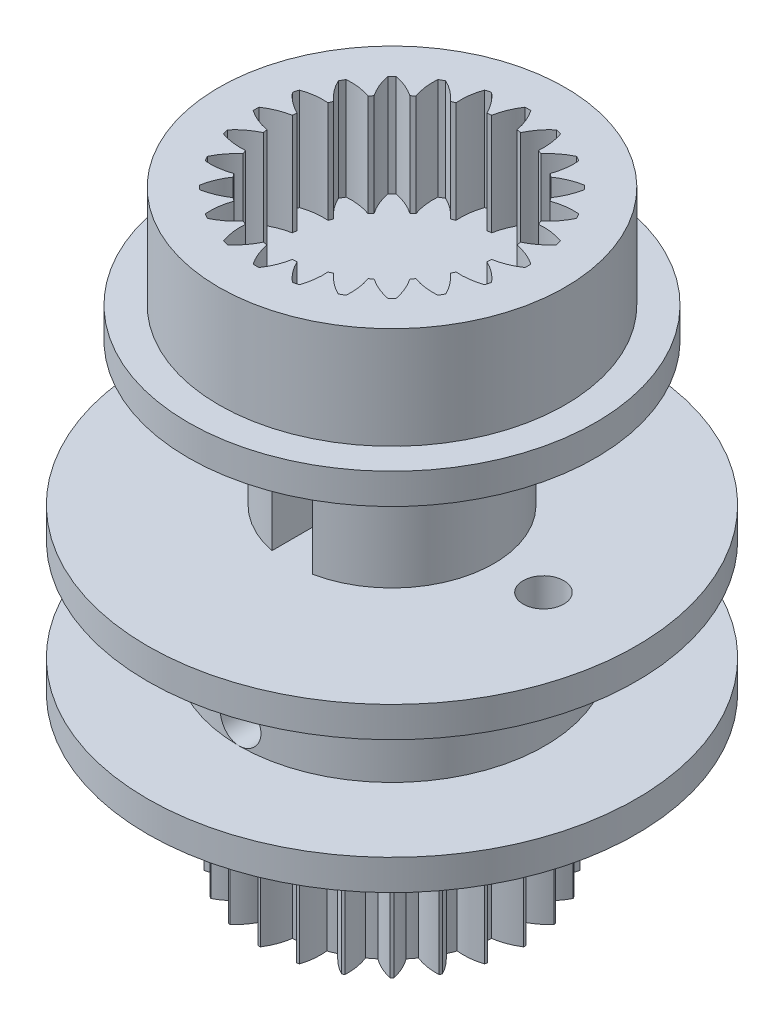
SolidWorks part; units mm, degrees
ref_plane "Front Plane" through (0, 0, 0) normal (0, 0, 1) x (1, 0, 0)
ref_plane "Top Plane" through (0, 0, 0) normal (0, 1, 0) x (1, 0, 0)
ref_plane "Right Plane" through (0, 0, 0) normal (1, 0, 0) x (0, 0, -1)
sketch "Sketch1" plane through (0, 0, 0) normal (0, 1, 0) x (1, 0, 0)
  arc A1 (17.6435, -5.4958) -> (17.2147, -6.6437) centre (20.0844, -7.0617) ccw
  arc A2 (17.2147, -6.6437) -> (16.7858, -6.7002) centre (17.7045, -12.0215) ccw
  arc A3 (16.7858, -6.7002) -> (16.0745, -5.7023) centre (14.122, -7.8467) ccw
  arc A4 (16.0745, -5.7023) -> (15.9566, -5.7339) centre (17.7045, -12.0215) ccw
  arc A5 (15.9566, -5.7339) -> (15.8395, -6.9538) centre (18.7196, -6.6147) ccw
  arc A6 (15.8395, -6.9538) -> (15.4399, -7.1193) centre (17.7045, -12.0215) ccw
  arc A7 (15.4399, -7.1193) -> (14.4945, -6.3396) centre (13.1636, -8.9161) ccw
  arc A8 (14.4945, -6.3396) -> (14.3888, -6.4005) centre (17.7045, -12.0215) ccw
  arc A9 (14.3888, -6.4005) -> (14.5914, -7.6091) centre (17.2857, -6.5362) ccw
  arc A10 (14.5914, -7.6091) -> (14.2483, -7.8725) centre (17.7045, -12.0215) ccw
  arc A11 (14.2483, -7.8725) -> (13.1333, -7.364) centre (12.5146, -10.1972) ccw
  arc A12 (13.1333, -7.364) -> (13.047, -7.4502) centre (17.7045, -12.0215) ccw
  arc A13 (13.047, -7.4502) -> (13.5555, -8.5652) centre (15.8802, -6.8315) ccw
  arc A14 (13.5555, -8.5652) -> (13.2922, -8.9084) centre (17.7045, -12.0215) ccw
  arc A15 (13.2922, -8.9084) -> (12.0836, -8.7058) centre (12.2193, -11.6026) ccw
  arc A16 (12.0836, -8.7058) -> (12.0226, -8.8114) centre (17.7045, -12.0215) ccw
  arc A17 (12.0226, -8.8114) -> (12.8023, -9.7568) centre (14.5992, -7.4805) ccw
  arc A18 (12.8023, -9.7568) -> (12.6368, -10.1565) centre (17.7045, -12.0215) ccw
  arc A19 (12.6368, -10.1565) -> (11.4169, -10.2736) centre (12.2978, -13.0366) ccw
  arc A20 (11.4169, -10.2736) -> (11.3854, -10.3914) centre (17.7045, -12.0215) ccw
  arc A21 (11.3854, -10.3914) -> (12.3832, -11.1028) centre (13.5297, -8.439) ccw
  arc A22 (12.3832, -11.1028) -> (12.3268, -11.5316) centre (17.7045, -12.0215) ccw
  arc A23 (12.3268, -11.5316) -> (11.1788, -11.9605) centre (12.7447, -14.4014) ccw
  arc A24 (11.1788, -11.9605) -> (11.1788, -12.0825) centre (17.7045, -12.0215) ccw
  arc A25 (11.1788, -12.0825) -> (12.3268, -12.5113) centre (12.7447, -9.6416) ccw
  arc A26 (12.3268, -12.5113) -> (12.3832, -12.9402) centre (17.7045, -12.0215) ccw
  arc A27 (12.3832, -12.9402) -> (11.3854, -13.6515) centre (13.5297, -15.604) ccw
  arc A28 (11.3854, -13.6515) -> (11.4169, -13.7694) centre (17.7045, -12.0215) ccw
  arc A29 (11.4169, -13.7694) -> (12.6368, -13.8865) centre (12.2978, -11.0064) ccw
  arc A30 (12.6368, -13.8865) -> (12.8023, -14.2861) centre (17.7045, -12.0215) ccw
  arc A31 (12.8023, -14.2861) -> (12.0226, -15.2315) centre (14.5992, -16.5624) ccw
  arc A32 (12.0226, -15.2315) -> (12.0836, -15.3372) centre (17.7045, -12.0215) ccw
  arc A33 (12.0836, -15.3372) -> (13.2922, -15.1346) centre (12.2193, -12.4403) ccw
  arc A34 (13.2922, -15.1346) -> (13.5555, -15.4777) centre (17.7045, -12.0215) ccw
  arc A35 (13.5555, -15.4777) -> (13.047, -16.5927) centre (15.8802, -17.2114) ccw
  arc A36 (13.047, -16.5927) -> (13.1333, -16.679) centre (17.7045, -12.0215) ccw
  arc A37 (13.1333, -16.679) -> (14.2483, -16.1705) centre (12.5146, -13.8458) ccw
  arc A38 (14.2483, -16.1705) -> (14.5914, -16.4338) centre (17.7045, -12.0215) ccw
  arc A39 (14.5914, -16.4338) -> (14.3888, -17.6424) centre (17.2857, -17.5067) ccw
  arc A40 (14.3888, -17.6424) -> (14.4945, -17.7034) centre (17.7045, -12.0215) ccw
  arc A41 (14.4945, -17.7034) -> (15.4399, -16.9237) centre (13.1636, -15.1268) ccw
  arc A42 (15.4399, -16.9237) -> (15.8395, -17.0892) centre (17.7045, -12.0215) ccw
  arc A43 (15.8395, -17.0892) -> (15.9566, -18.3091) centre (18.7196, -17.4282) ccw
  arc A44 (15.9566, -18.3091) -> (16.0745, -18.3406) centre (17.7045, -12.0215) ccw
  arc A45 (16.0745, -18.3406) -> (16.7858, -17.3428) centre (14.122, -16.1963) ccw
  arc A46 (16.7858, -17.3428) -> (17.2147, -17.3992) centre (17.7045, -12.0215) ccw
  arc A47 (17.2147, -17.3992) -> (17.6435, -18.5472) centre (20.0844, -16.9813) ccw
  arc A48 (17.6435, -18.5472) -> (17.7655, -18.5472) centre (17.7045, -12.0215) ccw
  arc A49 (17.7655, -18.5472) -> (18.1944, -17.3992) centre (15.3246, -16.9813) ccw
  arc A50 (18.1944, -17.3992) -> (18.6232, -17.3428) centre (17.7045, -12.0215) ccw
  arc A51 (18.6232, -17.3428) -> (19.3346, -18.3406) centre (21.287, -16.1963) ccw
  arc A52 (19.3346, -18.3406) -> (19.4524, -18.3091) centre (17.7045, -12.0215) ccw
  arc A53 (19.4524, -18.3091) -> (19.5695, -17.0892) centre (16.6894, -17.4282) ccw
  arc A54 (19.5695, -17.0892) -> (19.9692, -16.9237) centre (17.7045, -12.0215) ccw
  arc A55 (19.9692, -16.9237) -> (20.9146, -17.7034) centre (22.2455, -15.1268) ccw
  arc A56 (20.9146, -17.7034) -> (21.0202, -17.6424) centre (17.7045, -12.0215) ccw
  arc A57 (21.0202, -17.6424) -> (20.8176, -16.4338) centre (18.1234, -17.5067) ccw
  arc A58 (20.8176, -16.4338) -> (21.1608, -16.1705) centre (17.7045, -12.0215) ccw
  arc A59 (21.1608, -16.1705) -> (22.2758, -16.679) centre (22.8945, -13.8458) ccw
  arc A60 (22.2758, -16.679) -> (22.362, -16.5927) centre (17.7045, -12.0215) ccw
  arc A61 (22.362, -16.5927) -> (21.8535, -15.4777) centre (19.5288, -17.2114) ccw
  arc A62 (21.8535, -15.4777) -> (22.1169, -15.1346) centre (17.7045, -12.0215) ccw
  arc A63 (22.1169, -15.1346) -> (23.3255, -15.3372) centre (23.1898, -12.4403) ccw
  arc A64 (23.3255, -15.3372) -> (23.3864, -15.2315) centre (17.7045, -12.0215) ccw
  arc A65 (23.3864, -15.2315) -> (22.6067, -14.2861) centre (20.8099, -16.5624) ccw
  arc A66 (22.6067, -14.2861) -> (22.7722, -13.8865) centre (17.7045, -12.0215) ccw
  arc A67 (22.7722, -13.8865) -> (23.9921, -13.7694) centre (23.1113, -11.0064) ccw
  arc A68 (23.9921, -13.7694) -> (24.0237, -13.6515) centre (17.7045, -12.0215) ccw
  arc A69 (24.0237, -13.6515) -> (23.0258, -12.9402) centre (21.8793, -15.604) ccw
  arc A70 (23.0258, -12.9402) -> (23.0823, -12.5113) centre (17.7045, -12.0215) ccw
  arc A71 (23.0823, -12.5113) -> (24.2302, -12.0825) centre (22.6643, -9.6416) ccw
  arc A72 (24.2302, -12.0825) -> (24.2302, -11.9605) centre (17.7045, -12.0215) ccw
  arc A73 (24.2302, -11.9605) -> (23.0823, -11.5316) centre (22.6643, -14.4014) ccw
  arc A74 (23.0823, -11.5316) -> (23.0258, -11.1028) centre (17.7045, -12.0215) ccw
  arc A75 (23.0258, -11.1028) -> (24.0237, -10.3914) centre (21.8793, -8.439) ccw
  arc A76 (24.0237, -10.3914) -> (23.9921, -10.2736) centre (17.7045, -12.0215) ccw
  arc A77 (23.9921, -10.2736) -> (22.7722, -10.1565) centre (23.1113, -13.0366) ccw
  arc A78 (22.7722, -10.1565) -> (22.6067, -9.7568) centre (17.7045, -12.0215) ccw
  arc A79 (22.6067, -9.7568) -> (23.3864, -8.8114) centre (20.8099, -7.4805) ccw
  arc A80 (23.3864, -8.8114) -> (23.3255, -8.7058) centre (17.7045, -12.0215) ccw
  arc A81 (23.3255, -8.7058) -> (22.1169, -8.9084) centre (23.1898, -11.6026) ccw
  arc A82 (22.1169, -8.9084) -> (21.8535, -8.5652) centre (17.7045, -12.0215) ccw
  arc A83 (21.8535, -8.5652) -> (22.362, -7.4502) centre (19.5288, -6.8315) ccw
  arc A84 (22.362, -7.4502) -> (22.2758, -7.364) centre (17.7045, -12.0215) ccw
  arc A85 (22.2758, -7.364) -> (21.1608, -7.8725) centre (22.8945, -10.1972) ccw
  arc A86 (21.1608, -7.8725) -> (20.8176, -7.6091) centre (17.7045, -12.0215) ccw
  arc A87 (20.8176, -7.6091) -> (21.0202, -6.4005) centre (18.1234, -6.5362) ccw
  arc A88 (21.0202, -6.4005) -> (20.9146, -6.3396) centre (17.7045, -12.0215) ccw
  arc A89 (20.9146, -6.3396) -> (19.9692, -7.1193) centre (22.2455, -8.9161) ccw
  arc A90 (19.9692, -7.1193) -> (19.5695, -6.9538) centre (17.7045, -12.0215) ccw
  arc A91 (19.5695, -6.9538) -> (19.4524, -5.7339) centre (16.6894, -6.6147) ccw
  arc A92 (19.4524, -5.7339) -> (19.3346, -5.7023) centre (17.7045, -12.0215) ccw
  arc A93 (19.3346, -5.7023) -> (18.6232, -6.7002) centre (21.287, -7.8467) ccw
  arc A94 (18.6232, -6.7002) -> (18.1944, -6.6437) centre (17.7045, -12.0215) ccw
  arc A95 (18.1944, -6.6437) -> (17.7655, -5.4958) centre (15.3246, -7.0617) ccw
  arc A96 (17.7655, -5.4958) -> (17.6435, -5.4958) centre (17.7045, -12.0215) ccw
extrude "Boss-Extrude1" add sketch "Sketch1" along normal blind 7.5
sketch "Sketch2" plane through (0, 7.5, 0) normal (0, 1, 0) x (1, 0, 0)
  circle A0 centre (17.7045, -12.0215) radius 12
  dimension "D1" = 24
extrude "Boss-Extrude2" add sketch "Sketch2" along normal blind 1.5
sketch "Sketch3" plane through (0, 9, 0) normal (0, 1, 0) x (1, 0, 0)
  circle A0 centre (17.7045, -12.0215) radius 7.5
  dimension "D1" = 15
extrude "Boss-Extrude3" add sketch "Sketch3" along normal blind 5
sketch "Sketch4" plane through (0, 14, 0) normal (0, 1, 0) x (1, 0, 0)
  circle A0 centre (17.7045, -12.0215) radius 12
  dimension "D1" = 24
extrude "Boss-Extrude4" add sketch "Sketch4" along normal blind 1.5
sketch "Sketch6" plane through (0, 15.5, 0) normal (0, 1, 0) x (1, 0, 0)
  circle A1 centre (17.7045, -12.0215) radius 5
  dimension "D1" = 10
extrude "Boss-Extrude5" add sketch "Sketch6" along normal blind 7
sketch "Sketch9" plane through (0, 22.5, 0) normal (0, 1, 0) x (1, 0, 0)
  circle A0 centre (17.7045, -12.0215) radius 10
extrude "Boss-Extrude6" add sketch "Sketch9" along normal blind 1.5 contours A0
sketch "Sketch11" plane through (0, 24, 0) normal (0, 1, 0) x (1, 0, 0)
  arc A0 (17.847, -5.347) -> (17.562, -5.347) centre (17.7045, -12.0215) ccw
  arc A1 (17.562, -5.347) -> (17.0854, -6.5061) centre (20.0844, -7.0617) ccw
  arc A2 (17.0854, -6.5061) -> (16.875, -6.5338) centre (17.7045, -12.0215) ccw
  arc A3 (16.875, -6.5338) -> (16.1147, -5.5376) centre (14.122, -7.8467) ccw
  arc A4 (16.1147, -5.5376) -> (15.8394, -5.6113) centre (17.7045, -12.0215) ccw
  arc A5 (15.8394, -5.6113) -> (15.679, -6.8543) centre (18.7196, -6.6147) ccw
  arc A6 (15.679, -6.8543) -> (15.483, -6.9355) centre (17.7045, -12.0215) ccw
  arc A7 (15.483, -6.9355) -> (14.4907, -6.17) centre (13.1636, -8.9161) ccw
  arc A8 (14.4907, -6.17) -> (14.2439, -6.3125) centre (17.7045, -12.0215) ccw
  arc A9 (14.2439, -6.3125) -> (14.4107, -7.5546) centre (17.2857, -6.5362) ccw
  arc A10 (14.4107, -7.5546) -> (14.2423, -7.6838) centre (17.7045, -12.0215) ccw
  arc A11 (14.2423, -7.6838) -> (13.0857, -7.2012) centre (12.5146, -10.1972) ccw
  arc A12 (13.0857, -7.2012) -> (12.8842, -7.4027) centre (17.7045, -12.0215) ccw
  arc A13 (12.8842, -7.4027) -> (13.3668, -8.5593) centre (15.8802, -6.8315) ccw
  arc A14 (13.3668, -8.5593) -> (13.2376, -8.7277) centre (17.7045, -12.0215) ccw
  arc A15 (13.2376, -8.7277) -> (11.9955, -8.5608) centre (12.2193, -11.6026) ccw
  arc A16 (11.9955, -8.5608) -> (11.853, -8.8076) centre (17.7045, -12.0215) ccw
  arc A17 (11.853, -8.8076) -> (12.6185, -9.7999) centre (14.5992, -7.4805) ccw
  arc A18 (12.6185, -9.7999) -> (12.5373, -9.996) centre (17.7045, -12.0215) ccw
  arc A19 (12.5373, -9.996) -> (11.2943, -10.1564) centre (12.2978, -13.0366) ccw
  arc A20 (11.2943, -10.1564) -> (11.2206, -10.4316) centre (17.7045, -12.0215) ccw
  arc A21 (11.2206, -10.4316) -> (12.2169, -11.192) centre (13.5297, -8.439) ccw
  arc A22 (12.2169, -11.192) -> (12.1892, -11.4024) centre (17.7045, -12.0215) ccw
  arc A23 (12.1892, -11.4024) -> (11.03, -11.879) centre (12.7447, -14.4014) ccw
  arc A24 (11.03, -11.879) -> (11.03, -12.164) centre (17.7045, -12.0215) ccw
  arc A25 (11.03, -12.164) -> (12.1892, -12.6406) centre (12.7447, -9.6416) ccw
  arc A26 (12.1892, -12.6406) -> (12.2169, -12.851) centre (17.7045, -12.0215) ccw
  arc A27 (12.2169, -12.851) -> (11.2206, -13.6113) centre (13.5297, -15.604) ccw
  arc A28 (11.2206, -13.6113) -> (11.2943, -13.8866) centre (17.7045, -12.0215) ccw
  arc A29 (11.2943, -13.8866) -> (12.5373, -14.047) centre (12.2978, -11.0064) ccw
  arc A30 (12.5373, -14.047) -> (12.6185, -14.243) centre (17.7045, -12.0215) ccw
  arc A31 (12.6185, -14.243) -> (11.853, -15.2353) centre (14.5992, -16.5624) ccw
  arc A32 (11.853, -15.2353) -> (11.9955, -15.4821) centre (17.7045, -12.0215) ccw
  arc A33 (11.9955, -15.4821) -> (13.2376, -15.3153) centre (12.2193, -12.4403) ccw
  arc A34 (13.2376, -15.3153) -> (13.3668, -15.4837) centre (17.7045, -12.0215) ccw
  arc A35 (13.3668, -15.4837) -> (12.8842, -16.6403) centre (15.8802, -17.2114) ccw
  arc A36 (12.8842, -16.6403) -> (13.0857, -16.8418) centre (17.7045, -12.0215) ccw
  arc A37 (13.0857, -16.8418) -> (14.2423, -16.3592) centre (12.5146, -13.8458) ccw
  arc A38 (14.2423, -16.3592) -> (14.4107, -16.4884) centre (17.7045, -12.0215) ccw
  arc A39 (14.4107, -16.4884) -> (14.2439, -17.7305) centre (17.2857, -17.5067) ccw
  arc A40 (14.2439, -17.7305) -> (14.4907, -17.873) centre (17.7045, -12.0215) ccw
  arc A41 (14.4907, -17.873) -> (15.483, -17.1075) centre (13.1636, -15.1268) ccw
  arc A42 (15.483, -17.1075) -> (15.679, -17.1887) centre (17.7045, -12.0215) ccw
  arc A43 (15.679, -17.1887) -> (15.8394, -18.4317) centre (18.7196, -17.4282) ccw
  arc A44 (15.8394, -18.4317) -> (16.1147, -18.5054) centre (17.7045, -12.0215) ccw
  arc A45 (16.1147, -18.5054) -> (16.875, -17.5091) centre (14.122, -16.1963) ccw
  arc A46 (16.875, -17.5091) -> (17.0854, -17.5368) centre (17.7045, -12.0215) ccw
  arc A47 (17.0854, -17.5368) -> (17.562, -18.696) centre (20.0844, -16.9813) ccw
  arc A48 (17.562, -18.696) -> (17.847, -18.696) centre (17.7045, -12.0215) ccw
  arc A49 (17.847, -18.696) -> (18.3236, -17.5368) centre (15.3246, -16.9813) ccw
  arc A50 (18.3236, -17.5368) -> (18.534, -17.5091) centre (17.7045, -12.0215) ccw
  arc A51 (18.534, -17.5091) -> (19.2944, -18.5054) centre (21.287, -16.1963) ccw
  arc A52 (19.2944, -18.5054) -> (19.5696, -18.4317) centre (17.7045, -12.0215) ccw
  arc A53 (19.5696, -18.4317) -> (19.73, -17.1887) centre (16.6894, -17.4282) ccw
  arc A54 (19.73, -17.1887) -> (19.9261, -17.1075) centre (17.7045, -12.0215) ccw
  arc A55 (19.9261, -17.1075) -> (20.9184, -17.873) centre (22.2455, -15.1268) ccw
  arc A56 (20.9184, -17.873) -> (21.1652, -17.7305) centre (17.7045, -12.0215) ccw
  arc A57 (21.1652, -17.7305) -> (20.9983, -16.4884) centre (18.1234, -17.5067) ccw
  arc A58 (20.9983, -16.4884) -> (21.1667, -16.3592) centre (17.7045, -12.0215) ccw
  arc A59 (21.1667, -16.3592) -> (22.3233, -16.8418) centre (22.8945, -13.8458) ccw
  arc A60 (22.3233, -16.8418) -> (22.5248, -16.6403) centre (17.7045, -12.0215) ccw
  arc A61 (22.5248, -16.6403) -> (22.0422, -15.4837) centre (19.5288, -17.2114) ccw
  arc A62 (22.0422, -15.4837) -> (22.1714, -15.3153) centre (17.7045, -12.0215) ccw
  arc A63 (22.1714, -15.3153) -> (23.4135, -15.4821) centre (23.1898, -12.4403) ccw
  arc A64 (23.4135, -15.4821) -> (23.556, -15.2353) centre (17.7045, -12.0215) ccw
  arc A65 (23.556, -15.2353) -> (22.7905, -14.243) centre (20.8099, -16.5624) ccw
  arc A66 (22.7905, -14.243) -> (22.8717, -14.047) centre (17.7045, -12.0215) ccw
  arc A67 (22.8717, -14.047) -> (24.1147, -13.8866) centre (23.1113, -11.0064) ccw
  arc A68 (24.1147, -13.8866) -> (24.1884, -13.6113) centre (17.7045, -12.0215) ccw
  arc A69 (24.1884, -13.6113) -> (23.1922, -12.851) centre (21.8793, -15.604) ccw
  arc A70 (23.1922, -12.851) -> (23.2199, -12.6406) centre (17.7045, -12.0215) ccw
  arc A71 (23.2199, -12.6406) -> (24.379, -12.164) centre (22.6643, -9.6416) ccw
  arc A72 (24.379, -12.164) -> (24.379, -11.879) centre (17.7045, -12.0215) ccw
  arc A73 (24.379, -11.879) -> (23.2199, -11.4024) centre (22.6643, -14.4014) ccw
  arc A74 (23.2199, -11.4024) -> (23.1922, -11.192) centre (17.7045, -12.0215) ccw
  arc A75 (23.1922, -11.192) -> (24.1884, -10.4316) centre (21.8793, -8.439) ccw
  arc A76 (24.1884, -10.4316) -> (24.1147, -10.1564) centre (17.7045, -12.0215) ccw
  arc A77 (24.1147, -10.1564) -> (22.8717, -9.996) centre (23.1113, -13.0366) ccw
  arc A78 (22.8717, -9.996) -> (22.7905, -9.7999) centre (17.7045, -12.0215) ccw
  arc A79 (22.7905, -9.7999) -> (23.556, -8.8076) centre (20.8099, -7.4805) ccw
  arc A80 (23.556, -8.8076) -> (23.4135, -8.5608) centre (17.7045, -12.0215) ccw
  arc A81 (23.4135, -8.5608) -> (22.1714, -8.7277) centre (23.1898, -11.6026) ccw
  arc A82 (22.1714, -8.7277) -> (22.0422, -8.5593) centre (17.7045, -12.0215) ccw
  arc A83 (22.0422, -8.5593) -> (22.5248, -7.4027) centre (19.5288, -6.8315) ccw
  arc A84 (22.5248, -7.4027) -> (22.3233, -7.2012) centre (17.7045, -12.0215) ccw
  arc A85 (22.3233, -7.2012) -> (21.1667, -7.6838) centre (22.8945, -10.1972) ccw
  arc A86 (21.1667, -7.6838) -> (20.9983, -7.5546) centre (17.7045, -12.0215) ccw
  arc A87 (20.9983, -7.5546) -> (21.1652, -6.3125) centre (18.1234, -6.5362) ccw
  arc A88 (21.1652, -6.3125) -> (20.9184, -6.17) centre (17.7045, -12.0215) ccw
  arc A89 (20.9184, -6.17) -> (19.9261, -6.9355) centre (22.2455, -8.9161) ccw
  arc A90 (19.9261, -6.9355) -> (19.73, -6.8543) centre (17.7045, -12.0215) ccw
  arc A91 (19.73, -6.8543) -> (19.5696, -5.6113) centre (16.6894, -6.6147) ccw
  arc A92 (19.5696, -5.6113) -> (19.2944, -5.5376) centre (17.7045, -12.0215) ccw
  arc A93 (19.2944, -5.5376) -> (18.534, -6.5338) centre (21.287, -7.8467) ccw
  arc A94 (18.534, -6.5338) -> (18.3236, -6.5061) centre (17.7045, -12.0215) ccw
  arc A95 (18.3236, -6.5061) -> (17.847, -5.347) centre (15.3246, -7.0617) ccw
  arc A96 (17.7655, -5.4958) -> (17.6435, -5.4958) centre (17.7045, -12.0215) ccw
  arc A97 (18.1944, -6.6437) -> (17.7655, -5.4958) centre (15.3246, -7.0617) ccw
  arc A98 (18.6232, -6.7002) -> (18.1944, -6.6437) centre (17.7045, -12.0215) ccw
  arc A99 (19.3346, -5.7023) -> (18.6232, -6.7002) centre (21.287, -7.8467) ccw
  arc A100 (19.4524, -5.7339) -> (19.3346, -5.7023) centre (17.7045, -12.0215) ccw
  arc A101 (19.5695, -6.9538) -> (19.4524, -5.7339) centre (16.6894, -6.6147) ccw
  arc A102 (19.9692, -7.1193) -> (19.5695, -6.9538) centre (17.7045, -12.0215) ccw
  arc A103 (20.9146, -6.3396) -> (19.9692, -7.1193) centre (22.2455, -8.9161) ccw
  arc A104 (21.0202, -6.4005) -> (20.9146, -6.3396) centre (17.7045, -12.0215) ccw
  arc A105 (20.8176, -7.6091) -> (21.0202, -6.4005) centre (18.1234, -6.5362) ccw
  arc A106 (21.1608, -7.8725) -> (20.8176, -7.6091) centre (17.7045, -12.0215) ccw
  arc A107 (22.2758, -7.364) -> (21.1608, -7.8725) centre (22.8945, -10.1972) ccw
  arc A108 (22.362, -7.4502) -> (22.2758, -7.364) centre (17.7045, -12.0215) ccw
  arc A109 (21.8535, -8.5652) -> (22.362, -7.4502) centre (19.5288, -6.8315) ccw
  arc A110 (22.1169, -8.9084) -> (21.8535, -8.5652) centre (17.7045, -12.0215) ccw
  arc A111 (23.3255, -8.7058) -> (22.1169, -8.9084) centre (23.1898, -11.6026) ccw
  arc A112 (23.3864, -8.8114) -> (23.3255, -8.7058) centre (17.7045, -12.0215) ccw
  arc A113 (22.6067, -9.7568) -> (23.3864, -8.8114) centre (20.8099, -7.4805) ccw
  arc A114 (22.7722, -10.1565) -> (22.6067, -9.7568) centre (17.7045, -12.0215) ccw
  arc A115 (23.9921, -10.2736) -> (22.7722, -10.1565) centre (23.1113, -13.0366) ccw
  arc A116 (24.0237, -10.3914) -> (23.9921, -10.2736) centre (17.7045, -12.0215) ccw
  arc A117 (23.0258, -11.1028) -> (24.0237, -10.3914) centre (21.8793, -8.439) ccw
  arc A118 (23.0823, -11.5316) -> (23.0258, -11.1028) centre (17.7045, -12.0215) ccw
  arc A119 (24.2302, -11.9605) -> (23.0823, -11.5316) centre (22.6643, -14.4014) ccw
  arc A120 (24.2302, -12.0825) -> (24.2302, -11.9605) centre (17.7045, -12.0215) ccw
  arc A121 (23.0823, -12.5113) -> (24.2302, -12.0825) centre (22.6643, -9.6416) ccw
  arc A122 (23.0258, -12.9402) -> (23.0823, -12.5113) centre (17.7045, -12.0215) ccw
  arc A123 (24.0237, -13.6515) -> (23.0258, -12.9402) centre (21.8793, -15.604) ccw
  arc A124 (23.9921, -13.7694) -> (24.0237, -13.6515) centre (17.7045, -12.0215) ccw
  arc A125 (22.7722, -13.8865) -> (23.9921, -13.7694) centre (23.1113, -11.0064) ccw
  arc A126 (22.6067, -14.2861) -> (22.7722, -13.8865) centre (17.7045, -12.0215) ccw
  arc A127 (23.3864, -15.2315) -> (22.6067, -14.2861) centre (20.8099, -16.5624) ccw
  arc A128 (23.3255, -15.3372) -> (23.3864, -15.2315) centre (17.7045, -12.0215) ccw
  arc A129 (22.1169, -15.1346) -> (23.3255, -15.3372) centre (23.1898, -12.4403) ccw
  arc A130 (21.8535, -15.4777) -> (22.1169, -15.1346) centre (17.7045, -12.0215) ccw
  arc A131 (22.362, -16.5927) -> (21.8535, -15.4777) centre (19.5288, -17.2114) ccw
  arc A132 (22.2758, -16.679) -> (22.362, -16.5927) centre (17.7045, -12.0215) ccw
  arc A133 (21.1608, -16.1705) -> (22.2758, -16.679) centre (22.8945, -13.8458) ccw
  arc A134 (20.8176, -16.4338) -> (21.1608, -16.1705) centre (17.7045, -12.0215) ccw
  arc A135 (21.0202, -17.6424) -> (20.8176, -16.4338) centre (18.1234, -17.5067) ccw
  arc A136 (20.9146, -17.7034) -> (21.0202, -17.6424) centre (17.7045, -12.0215) ccw
  arc A137 (19.9692, -16.9237) -> (20.9146, -17.7034) centre (22.2455, -15.1268) ccw
  arc A138 (19.5695, -17.0892) -> (19.9692, -16.9237) centre (17.7045, -12.0215) ccw
  arc A139 (19.4524, -18.3091) -> (19.5695, -17.0892) centre (16.6894, -17.4282) ccw
  arc A140 (19.3346, -18.3406) -> (19.4524, -18.3091) centre (17.7045, -12.0215) ccw
  arc A141 (18.6232, -17.3428) -> (19.3346, -18.3406) centre (21.287, -16.1963) ccw
  arc A142 (18.1944, -17.3992) -> (18.6232, -17.3428) centre (17.7045, -12.0215) ccw
  arc A143 (17.7655, -18.5472) -> (18.1944, -17.3992) centre (15.3246, -16.9813) ccw
  arc A144 (17.6435, -18.5472) -> (17.7655, -18.5472) centre (17.7045, -12.0215) ccw
  arc A145 (17.2147, -17.3992) -> (17.6435, -18.5472) centre (20.0844, -16.9813) ccw
  arc A146 (16.7858, -17.3428) -> (17.2147, -17.3992) centre (17.7045, -12.0215) ccw
  arc A147 (16.0745, -18.3406) -> (16.7858, -17.3428) centre (14.122, -16.1963) ccw
  arc A148 (15.9566, -18.3091) -> (16.0745, -18.3406) centre (17.7045, -12.0215) ccw
  arc A149 (15.8395, -17.0892) -> (15.9566, -18.3091) centre (18.7196, -17.4282) ccw
  arc A150 (15.4399, -16.9237) -> (15.8395, -17.0892) centre (17.7045, -12.0215) ccw
  arc A151 (14.4945, -17.7034) -> (15.4399, -16.9237) centre (13.1636, -15.1268) ccw
  arc A152 (14.3888, -17.6424) -> (14.4945, -17.7034) centre (17.7045, -12.0215) ccw
  arc A153 (14.5914, -16.4338) -> (14.3888, -17.6424) centre (17.2857, -17.5067) ccw
  arc A154 (14.2483, -16.1705) -> (14.5914, -16.4338) centre (17.7045, -12.0215) ccw
  arc A155 (13.1333, -16.679) -> (14.2483, -16.1705) centre (12.5146, -13.8458) ccw
  arc A156 (13.047, -16.5927) -> (13.1333, -16.679) centre (17.7045, -12.0215) ccw
  arc A157 (13.5555, -15.4777) -> (13.047, -16.5927) centre (15.8802, -17.2114) ccw
  arc A158 (13.2922, -15.1346) -> (13.5555, -15.4777) centre (17.7045, -12.0215) ccw
  arc A159 (12.0836, -15.3372) -> (13.2922, -15.1346) centre (12.2193, -12.4403) ccw
  arc A160 (12.0226, -15.2315) -> (12.0836, -15.3372) centre (17.7045, -12.0215) ccw
  arc A161 (12.8023, -14.2861) -> (12.0226, -15.2315) centre (14.5992, -16.5624) ccw
  arc A162 (12.6368, -13.8865) -> (12.8023, -14.2861) centre (17.7045, -12.0215) ccw
  arc A163 (11.4169, -13.7694) -> (12.6368, -13.8865) centre (12.2978, -11.0064) ccw
  arc A164 (11.3854, -13.6515) -> (11.4169, -13.7694) centre (17.7045, -12.0215) ccw
  arc A165 (12.3832, -12.9402) -> (11.3854, -13.6515) centre (13.5297, -15.604) ccw
  arc A166 (12.3268, -12.5113) -> (12.3832, -12.9402) centre (17.7045, -12.0215) ccw
  arc A167 (11.1788, -12.0825) -> (12.3268, -12.5113) centre (12.7447, -9.6416) ccw
  arc A168 (11.1788, -11.9605) -> (11.1788, -12.0825) centre (17.7045, -12.0215) ccw
  arc A169 (12.3268, -11.5316) -> (11.1788, -11.9605) centre (12.7447, -14.4014) ccw
  arc A170 (12.3832, -11.1028) -> (12.3268, -11.5316) centre (17.7045, -12.0215) ccw
  arc A171 (11.3854, -10.3914) -> (12.3832, -11.1028) centre (13.5297, -8.439) ccw
  arc A172 (11.4169, -10.2736) -> (11.3854, -10.3914) centre (17.7045, -12.0215) ccw
  arc A173 (12.6368, -10.1565) -> (11.4169, -10.2736) centre (12.2978, -13.0366) ccw
  arc A174 (12.8023, -9.7568) -> (12.6368, -10.1565) centre (17.7045, -12.0215) ccw
  arc A175 (12.0226, -8.8114) -> (12.8023, -9.7568) centre (14.5992, -7.4805) ccw
  arc A176 (12.0836, -8.7058) -> (12.0226, -8.8114) centre (17.7045, -12.0215) ccw
  arc A177 (13.2922, -8.9084) -> (12.0836, -8.7058) centre (12.2193, -11.6026) ccw
  arc A178 (13.5555, -8.5652) -> (13.2922, -8.9084) centre (17.7045, -12.0215) ccw
  arc A179 (13.047, -7.4502) -> (13.5555, -8.5652) centre (15.8802, -6.8315) ccw
  arc A180 (13.1333, -7.364) -> (13.047, -7.4502) centre (17.7045, -12.0215) ccw
  arc A181 (14.2483, -7.8725) -> (13.1333, -7.364) centre (12.5146, -10.1972) ccw
  arc A182 (14.5914, -7.6091) -> (14.2483, -7.8725) centre (17.7045, -12.0215) ccw
  arc A183 (14.3888, -6.4005) -> (14.5914, -7.6091) centre (17.2857, -6.5362) ccw
  arc A184 (14.4945, -6.3396) -> (14.3888, -6.4005) centre (17.7045, -12.0215) ccw
  arc A185 (15.4399, -7.1193) -> (14.4945, -6.3396) centre (13.1636, -8.9161) ccw
  arc A186 (15.8395, -6.9538) -> (15.4399, -7.1193) centre (17.7045, -12.0215) ccw
  arc A187 (15.9566, -5.7339) -> (15.8395, -6.9538) centre (18.7196, -6.6147) ccw
  arc A188 (16.0745, -5.7023) -> (15.9566, -5.7339) centre (17.7045, -12.0215) ccw
  arc A189 (16.7858, -6.7002) -> (16.0745, -5.7023) centre (14.122, -7.8467) ccw
  arc A190 (17.2147, -6.6437) -> (16.7858, -6.7002) centre (17.7045, -12.0215) ccw
  arc A191 (17.6435, -5.4958) -> (17.2147, -6.6437) centre (20.0844, -7.0617) ccw
  arc A192 (17.7655, -5.4958) -> (17.6435, -5.4958) centre (17.7045, -12.0215) ccw construction
  arc A193 (18.1944, -6.6437) -> (17.7655, -5.4958) centre (15.3246, -7.0617) ccw construction
  arc A194 (18.6232, -6.7002) -> (18.1944, -6.6437) centre (17.7045, -12.0215) ccw construction
  arc A195 (19.3346, -5.7023) -> (18.6232, -6.7002) centre (21.287, -7.8467) ccw construction
  arc A196 (19.4524, -5.7339) -> (19.3346, -5.7023) centre (17.7045, -12.0215) ccw construction
  arc A197 (19.5695, -6.9538) -> (19.4524, -5.7339) centre (16.6894, -6.6147) ccw construction
  arc A198 (19.9692, -7.1193) -> (19.5695, -6.9538) centre (17.7045, -12.0215) ccw construction
  arc A199 (20.9146, -6.3396) -> (19.9692, -7.1193) centre (22.2455, -8.9161) ccw construction
  arc A200 (21.0202, -6.4005) -> (20.9146, -6.3396) centre (17.7045, -12.0215) ccw construction
  arc A201 (20.8176, -7.6091) -> (21.0202, -6.4005) centre (18.1234, -6.5362) ccw construction
  arc A202 (21.1608, -7.8725) -> (20.8176, -7.6091) centre (17.7045, -12.0215) ccw construction
  arc A203 (22.2758, -7.364) -> (21.1608, -7.8725) centre (22.8945, -10.1972) ccw construction
  arc A204 (22.362, -7.4502) -> (22.2758, -7.364) centre (17.7045, -12.0215) ccw construction
  arc A205 (21.8535, -8.5652) -> (22.362, -7.4502) centre (19.5288, -6.8315) ccw construction
  arc A206 (22.1169, -8.9084) -> (21.8535, -8.5652) centre (17.7045, -12.0215) ccw construction
  arc A207 (23.3255, -8.7058) -> (22.1169, -8.9084) centre (23.1898, -11.6026) ccw construction
  arc A208 (23.3864, -8.8114) -> (23.3255, -8.7058) centre (17.7045, -12.0215) ccw construction
  arc A209 (22.6067, -9.7568) -> (23.3864, -8.8114) centre (20.8099, -7.4805) ccw construction
  arc A210 (22.7722, -10.1565) -> (22.6067, -9.7568) centre (17.7045, -12.0215) ccw construction
  arc A211 (23.9921, -10.2736) -> (22.7722, -10.1565) centre (23.1113, -13.0366) ccw construction
  arc A212 (24.0237, -10.3914) -> (23.9921, -10.2736) centre (17.7045, -12.0215) ccw construction
  arc A213 (23.0258, -11.1028) -> (24.0237, -10.3914) centre (21.8793, -8.439) ccw construction
  arc A214 (23.0823, -11.5316) -> (23.0258, -11.1028) centre (17.7045, -12.0215) ccw construction
  arc A215 (24.2302, -11.9605) -> (23.0823, -11.5316) centre (22.6643, -14.4014) ccw construction
  arc A216 (24.2302, -12.0825) -> (24.2302, -11.9605) centre (17.7045, -12.0215) ccw construction
  arc A217 (23.0823, -12.5113) -> (24.2302, -12.0825) centre (22.6643, -9.6416) ccw construction
  arc A218 (23.0258, -12.9402) -> (23.0823, -12.5113) centre (17.7045, -12.0215) ccw construction
  arc A219 (24.0237, -13.6515) -> (23.0258, -12.9402) centre (21.8793, -15.604) ccw construction
  arc A220 (23.9921, -13.7694) -> (24.0237, -13.6515) centre (17.7045, -12.0215) ccw construction
  arc A221 (22.7722, -13.8865) -> (23.9921, -13.7694) centre (23.1113, -11.0064) ccw construction
  arc A222 (22.6067, -14.2861) -> (22.7722, -13.8865) centre (17.7045, -12.0215) ccw construction
  arc A223 (23.3864, -15.2315) -> (22.6067, -14.2861) centre (20.8099, -16.5624) ccw construction
  arc A224 (23.3255, -15.3372) -> (23.3864, -15.2315) centre (17.7045, -12.0215) ccw construction
  arc A225 (22.1169, -15.1346) -> (23.3255, -15.3372) centre (23.1898, -12.4403) ccw construction
  arc A226 (21.8535, -15.4777) -> (22.1169, -15.1346) centre (17.7045, -12.0215) ccw construction
  arc A227 (22.362, -16.5927) -> (21.8535, -15.4777) centre (19.5288, -17.2114) ccw construction
  arc A228 (22.2758, -16.679) -> (22.362, -16.5927) centre (17.7045, -12.0215) ccw construction
  arc A229 (21.1608, -16.1705) -> (22.2758, -16.679) centre (22.8945, -13.8458) ccw construction
  arc A230 (20.8176, -16.4338) -> (21.1608, -16.1705) centre (17.7045, -12.0215) ccw construction
  arc A231 (21.0202, -17.6424) -> (20.8176, -16.4338) centre (18.1234, -17.5067) ccw construction
  arc A232 (20.9146, -17.7034) -> (21.0202, -17.6424) centre (17.7045, -12.0215) ccw construction
  arc A233 (19.9692, -16.9237) -> (20.9146, -17.7034) centre (22.2455, -15.1268) ccw construction
  arc A234 (19.5695, -17.0892) -> (19.9692, -16.9237) centre (17.7045, -12.0215) ccw construction
  arc A235 (19.4524, -18.3091) -> (19.5695, -17.0892) centre (16.6894, -17.4282) ccw construction
  arc A236 (19.3346, -18.3406) -> (19.4524, -18.3091) centre (17.7045, -12.0215) ccw construction
  arc A237 (18.6232, -17.3428) -> (19.3346, -18.3406) centre (21.287, -16.1963) ccw construction
  arc A238 (18.1944, -17.3992) -> (18.6232, -17.3428) centre (17.7045, -12.0215) ccw construction
  arc A239 (17.7655, -18.5472) -> (18.1944, -17.3992) centre (15.3246, -16.9813) ccw construction
  arc A240 (17.6435, -18.5472) -> (17.7655, -18.5472) centre (17.7045, -12.0215) ccw construction
  arc A241 (17.2147, -17.3992) -> (17.6435, -18.5472) centre (20.0844, -16.9813) ccw construction
  arc A242 (16.7858, -17.3428) -> (17.2147, -17.3992) centre (17.7045, -12.0215) ccw construction
  arc A243 (16.0745, -18.3406) -> (16.7858, -17.3428) centre (14.122, -16.1963) ccw construction
  arc A244 (15.9566, -18.3091) -> (16.0745, -18.3406) centre (17.7045, -12.0215) ccw construction
  arc A245 (15.8395, -17.0892) -> (15.9566, -18.3091) centre (18.7196, -17.4282) ccw construction
  arc A246 (15.4399, -16.9237) -> (15.8395, -17.0892) centre (17.7045, -12.0215) ccw construction
  arc A247 (14.4945, -17.7034) -> (15.4399, -16.9237) centre (13.1636, -15.1268) ccw construction
  arc A248 (14.3888, -17.6424) -> (14.4945, -17.7034) centre (17.7045, -12.0215) ccw construction
  arc A249 (14.5914, -16.4338) -> (14.3888, -17.6424) centre (17.2857, -17.5067) ccw construction
  arc A250 (14.2483, -16.1705) -> (14.5914, -16.4338) centre (17.7045, -12.0215) ccw construction
  arc A251 (13.1333, -16.679) -> (14.2483, -16.1705) centre (12.5146, -13.8458) ccw construction
  arc A252 (13.047, -16.5927) -> (13.1333, -16.679) centre (17.7045, -12.0215) ccw construction
  arc A253 (13.5555, -15.4777) -> (13.047, -16.5927) centre (15.8802, -17.2114) ccw construction
  arc A254 (13.2922, -15.1346) -> (13.5555, -15.4777) centre (17.7045, -12.0215) ccw construction
  arc A255 (12.0836, -15.3372) -> (13.2922, -15.1346) centre (12.2193, -12.4403) ccw construction
  arc A256 (12.0226, -15.2315) -> (12.0836, -15.3372) centre (17.7045, -12.0215) ccw construction
  arc A257 (12.8023, -14.2861) -> (12.0226, -15.2315) centre (14.5992, -16.5624) ccw construction
  arc A258 (12.6368, -13.8865) -> (12.8023, -14.2861) centre (17.7045, -12.0215) ccw construction
  arc A259 (11.4169, -13.7694) -> (12.6368, -13.8865) centre (12.2978, -11.0064) ccw construction
  arc A260 (11.3854, -13.6515) -> (11.4169, -13.7694) centre (17.7045, -12.0215) ccw construction
  arc A261 (12.3832, -12.9402) -> (11.3854, -13.6515) centre (13.5297, -15.604) ccw construction
  arc A262 (12.3268, -12.5113) -> (12.3832, -12.9402) centre (17.7045, -12.0215) ccw construction
  arc A263 (11.1788, -12.0825) -> (12.3268, -12.5113) centre (12.7447, -9.6416) ccw construction
  arc A264 (11.1788, -11.9605) -> (11.1788, -12.0825) centre (17.7045, -12.0215) ccw construction
  arc A265 (12.3268, -11.5316) -> (11.1788, -11.9605) centre (12.7447, -14.4014) ccw construction
  arc A266 (12.3832, -11.1028) -> (12.3268, -11.5316) centre (17.7045, -12.0215) ccw construction
  arc A267 (11.3854, -10.3914) -> (12.3832, -11.1028) centre (13.5297, -8.439) ccw construction
  arc A268 (11.4169, -10.2736) -> (11.3854, -10.3914) centre (17.7045, -12.0215) ccw construction
  arc A269 (12.6368, -10.1565) -> (11.4169, -10.2736) centre (12.2978, -13.0366) ccw construction
  arc A270 (12.8023, -9.7568) -> (12.6368, -10.1565) centre (17.7045, -12.0215) ccw construction
  arc A271 (12.0226, -8.8114) -> (12.8023, -9.7568) centre (14.5992, -7.4805) ccw construction
  arc A272 (12.0836, -8.7058) -> (12.0226, -8.8114) centre (17.7045, -12.0215) ccw construction
  arc A273 (13.2922, -8.9084) -> (12.0836, -8.7058) centre (12.2193, -11.6026) ccw construction
  arc A274 (13.5555, -8.5652) -> (13.2922, -8.9084) centre (17.7045, -12.0215) ccw construction
  arc A275 (13.047, -7.4502) -> (13.5555, -8.5652) centre (15.8802, -6.8315) ccw construction
  arc A276 (13.1333, -7.364) -> (13.047, -7.4502) centre (17.7045, -12.0215) ccw construction
  arc A277 (14.2483, -7.8725) -> (13.1333, -7.364) centre (12.5146, -10.1972) ccw construction
  arc A278 (14.5914, -7.6091) -> (14.2483, -7.8725) centre (17.7045, -12.0215) ccw construction
  arc A279 (14.3888, -6.4005) -> (14.5914, -7.6091) centre (17.2857, -6.5362) ccw construction
  arc A280 (14.4945, -6.3396) -> (14.3888, -6.4005) centre (17.7045, -12.0215) ccw construction
  arc A281 (15.4399, -7.1193) -> (14.4945, -6.3396) centre (13.1636, -8.9161) ccw construction
  arc A282 (15.8395, -6.9538) -> (15.4399, -7.1193) centre (17.7045, -12.0215) ccw construction
  arc A283 (15.9566, -5.7339) -> (15.8395, -6.9538) centre (18.7196, -6.6147) ccw construction
  arc A284 (16.0745, -5.7023) -> (15.9566, -5.7339) centre (17.7045, -12.0215) ccw construction
  arc A285 (16.7858, -6.7002) -> (16.0745, -5.7023) centre (14.122, -7.8467) ccw construction
  arc A286 (17.2147, -6.6437) -> (16.7858, -6.7002) centre (17.7045, -12.0215) ccw construction
  arc A287 (17.6435, -5.4958) -> (17.2147, -6.6437) centre (20.0844, -7.0617) ccw construction
  circle A290 centre (17.7045, -12.0215) radius 8.5
  dimension "D1" = 0
  dimension "D2" = 0.15
extrude "Boss-Extrude7" add sketch "Sketch11" along normal blind 5
sketch "Sketch7" plane through (0, 0, 0) normal (0, 0, 1) x (1, 0, 0)
  line L0 (7.7045, 22.5) -> (27.7045, 22.5) construction
  line L8 (7.7045, 22.5) -> (27.7045, 22.5) construction
  line L9 (29.7045, 15.5) -> (5.7045, 15.5) construction
  line L10 (17.7045, 22.5) -> (17.7045, 15.5) construction
  line L11 (17.7045, 14) -> (17.7045, 9) construction
  line L12 (10.2045, 14) -> (25.2045, 14) construction
  line L13 (29.7045, 9) -> (5.7045, 9) construction
  line L14 (29.7045, 9) -> (5.7045, 9) construction
  line L15 (29.7045, 15.5) -> (5.7045, 15.5) construction
  line L17 (16.7045, 22.5) -> (18.7045, 22.5)
  line L18 (16.7045, 22.5) -> (16.7045, 15.5)
  line L19 (16.7045, 15.5) -> (18.7045, 15.5)
  line L20 (18.7045, 22.5) -> (18.7045, 15.5)
  line L21 (16.7045, 22.5) -> (18.7045, 15.5) construction
  line L22 (16.7045, 15.5) -> (18.7045, 22.5) construction
  circle A2 centre (17.7045, 10) radius 1
  point P7 (17.7045, 19)
  dimension "D2" = 2
  dimension "D1" = 2
extrude "Cut-Extrude1" cut sketch "Sketch7" along normal through all
sketch "Sketch13" plane through (0, 14, 0) normal (0, 1, 0) x (1, 0, 0)
  line L0 (17.7045, -12.0215) -> (25.1415, -12.0215) construction
  circle A0 centre (25.1415, -12.0215) radius 1
extrude "Cut-Extrude2" cut sketch "Sketch13" along normal blind 4
